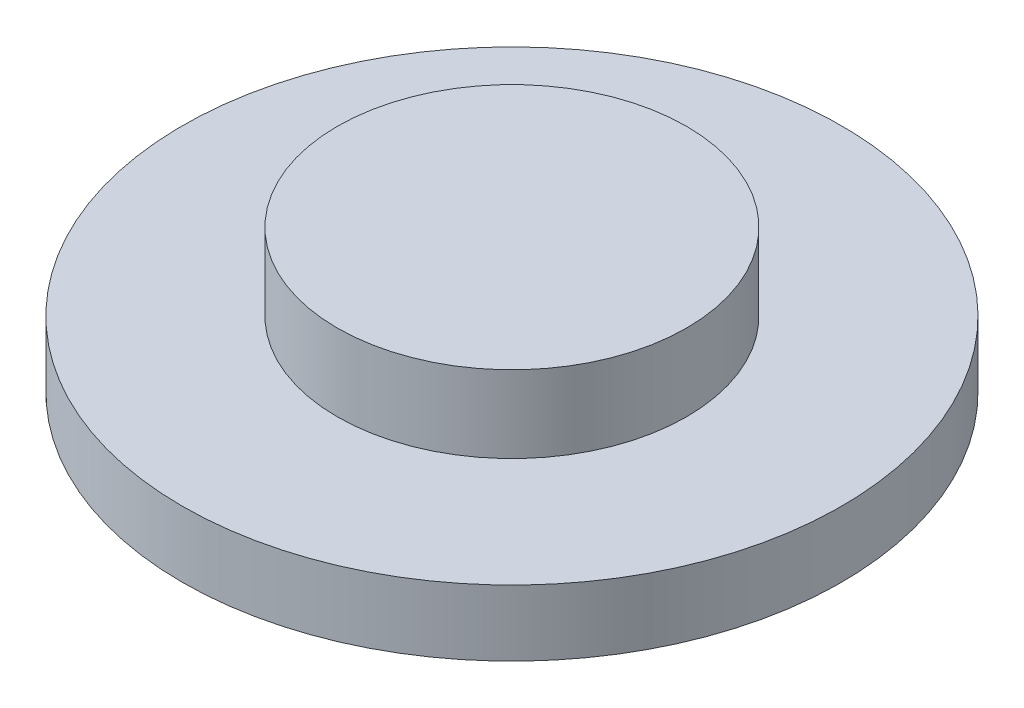
SolidWorks part; units mm, degrees
ref_plane "前视基准面" through (0, 0, 0) normal (0, 0, 1) x (1, 0, 0)
ref_plane "上视基准面" through (0, 0, 0) normal (0, 1, 0) x (1, 0, 0)
ref_plane "右视基准面" through (0, 0, 0) normal (1, 0, 0) x (0, 0, -1)
other "Configuration Table"
sketch "草图1" plane through (0, 0, 0) normal (0, 1, 0) x (1, 0, 0)
  circle A0 centre (0, 0) radius 15
  dimension "D1" = 30
extrude "凸台-拉伸1" add sketch "草图1" along normal blind 3
sketch "草图2" plane through (0, 3, 0) normal (0, 1, 0) x (1, 0, 0)
  circle A0 centre (0, 0) radius 7.95
  dimension "D1" = 15.9
extrude "凸台-拉伸2" add sketch "草图2" along normal blind 3.5
